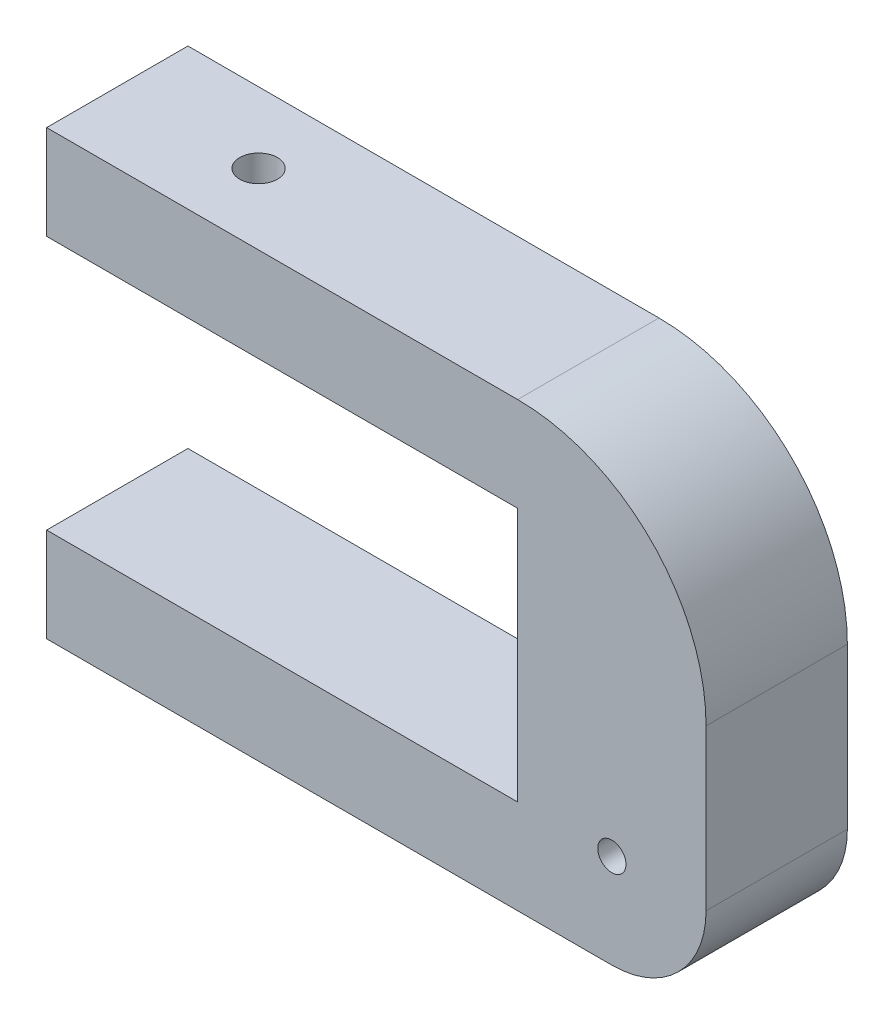
SolidWorks part; units mm, degrees
ref_plane "Plan de face" through (0, 0, 0) normal (0, 0, 1) x (1, 0, 0)
ref_plane "Plan de dessus" through (0, 0, 0) normal (0, 1, 0) x (1, 0, 0)
ref_plane "Plan de droite" through (0, 0, 0) normal (1, 0, 0) x (0, 0, -1)
sketch "Esquisse1" plane through (0, 0, 0) normal (0, 0, 1) x (1, 0, 0)
  line L0 (0, 0) -> (50, 0)
  line L1 (0, -47) -> (60, -47)
  line L2 (70, -20) -> (70, -37)
  line L3 (0, -47) -> (0, -37)
  line L4 (0, -37) -> (50, -37)
  line L5 (50, -37) -> (50, -10)
  line L6 (50, -10) -> (0, -10)
  line L7 (0, -10) -> (0, 0)
  arc A0 (50, 0) -> (70, -20) centre (50, -20) cw
  arc A1 (70, -37) -> (60, -47) centre (60, -37) cw
  circle A2 centre (60, -37) radius 1.5
  dimension "D4" = 20
  dimension "D1" = 10
  dimension "D2" = 10
  dimension "D3" = 27
  dimension "D5" = 50
extrude "Boss.-Extru.1" add sketch "Esquisse1" along normal blind 15
sketch "Esquisse3" plane through (0, -10, 0) normal (0, -1, 0) x (1, 0, 0)
  line L0 (0, 15) -> (0, 0) construction
  line L1 (0, 15) -> (50, 15) construction
  circle A0 centre (15, 7.5) radius 5
  dimension "D1" = 15
  dimension "D2" = 7.5
extrude "Enlèv. mat.-Extru.1" cut sketch "Esquisse3" against normal blind 2
sketch "Esquisse4" plane through (0, -8, 0) normal (0, -1, 0) x (-1, 0, 0)
  circle A0 centre (-15, -7.5) radius 2
  circle A1 centre (-15, -7.5) radius 5 construction
  circle A2 centre (-15, -7.5) radius 5 construction
  dimension "D1" = 0
  dimension "D2" = 0
extrude "Enlèv. mat.-Extru.2" cut sketch "Esquisse4" against normal through all
sketch "Esquisse5" plane through (0, -8, 0) normal (0, -1, 0) x (1, 0, 0)
  line L0 (15, 7.5) -> (11.0834, 7.5) construction
  line L1 (12.5, 7.5) -> (12.5, 9.5984) construction
  line L2 (12.5, 7.5) -> (12.5, 5.6421) construction
  line L3 (13.75, 9.6651) -> (12.141, 8.7361) construction
  line L4 (15, 7.5) -> (13.0417, 10.8918) construction
  line L5 (13.75, 9.6651) -> (15.5673, 10.7143) construction
  line L6 (16.25, 9.6651) -> (14.641, 10.594) construction
  line L7 (15, 7.5) -> (16.9583, 10.8918) construction
  line L8 (16.25, 9.6651) -> (18.0673, 8.6159) construction
  line L9 (17.5, 7.5) -> (17.5, 9.3579) construction
  line L10 (15, 7.5) -> (18.9166, 7.5) construction
  line L11 (17.5, 7.5) -> (17.5, 5.4016) construction
  line L12 (16.25, 5.3349) -> (17.859, 6.2639) construction
  line L13 (15, 7.5) -> (16.9583, 4.1082) construction
  line L14 (16.25, 5.3349) -> (14.4327, 4.2857) construction
  line L15 (13.75, 5.3349) -> (15.359, 4.406) construction
  line L16 (15, 7.5) -> (13.0417, 4.1082) construction
  line L17 (13.75, 5.3349) -> (11.9327, 6.3841) construction
  line L18 (12.5, 6.0566) -> (12.5, 8.9434)
  line L19 (12.5, 8.9434) -> (15, 10.3868)
  line L20 (15, 10.3868) -> (17.5, 8.9434)
  line L21 (17.5, 8.9434) -> (17.5, 6.0566)
  line L22 (17.5, 6.0566) -> (15, 4.6132)
  line L23 (15, 4.6132) -> (12.5, 6.0566)
  circle A0 centre (15, 7.5) radius 2 construction
  point P28 (15, 7.5)
  dimension "D2" = 0
  dimension "D1" = 6
extrude "Enlèv. mat.-Extru.3" cut sketch "Esquisse5" against normal blind 2.5
